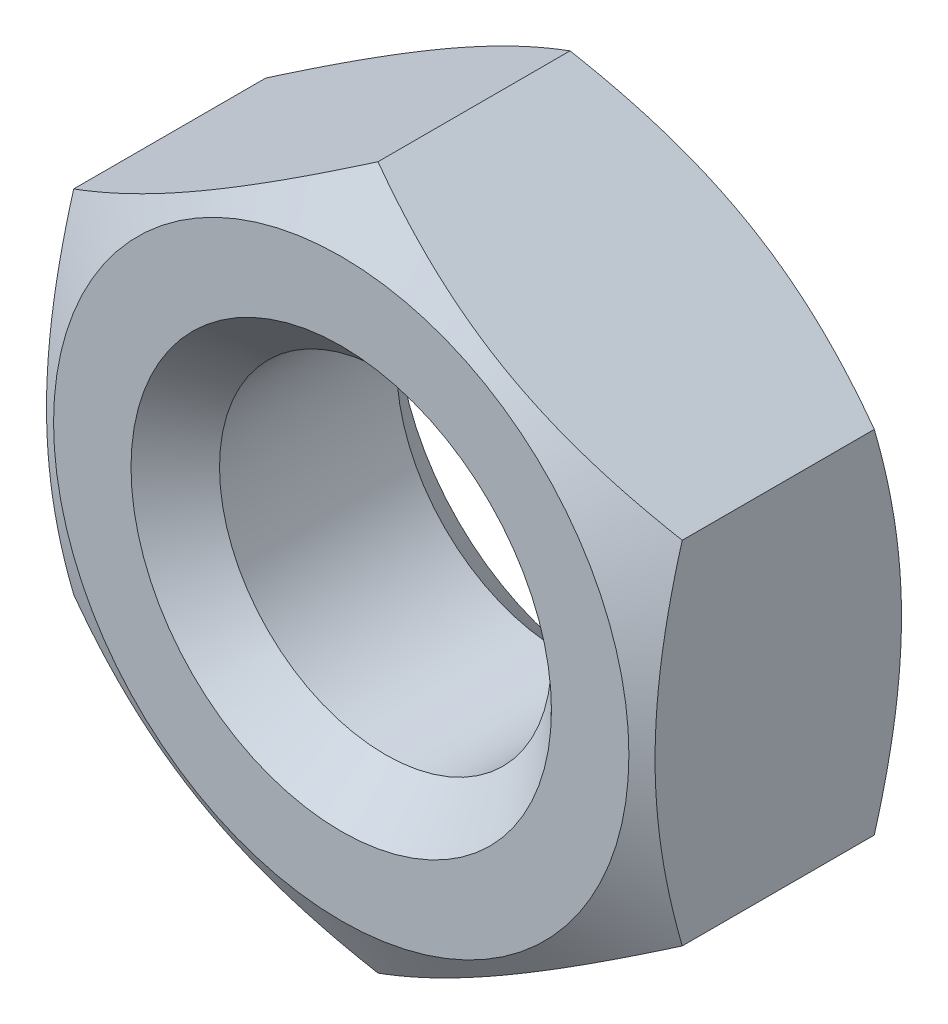
SolidWorks part; units mm, degrees
material "Простая углеродистая сталь"
ref_plane "Спереди" through (0, 0, 0) normal (0, 0, 1) x (1, 0, 0)
ref_plane "Сверху" through (0, 0, 0) normal (0, 1, 0) x (1, 0, 0)
ref_plane "Справа" through (0, 0, 0) normal (1, 0, 0) x (0, 0, -1)
sketch "Эскиз1" plane through (0, 0, 0) normal (0, 1, 0) x (1, 0, 0)
  line L1 (0, 0) -> (-4, 0)
  line L2 (0, 0) -> (0, 2.4)
  line L3 (0, 2.4) -> (-4, 2.4)
  line L4 (-4, 0) -> (-4, 2.4)
  dimension "D1" = 2.4
  dimension "D2" = 4
revolve "Повернуть1" add sketch "Эскиз1" angle 360 about L2
sketch "Эскиз2" plane through (0, 0, 0) normal (0, 0, 1) x (1, 0, 0)
  line L7 (2.75, -1.5877) -> (2.75, 1.5877)
  line L8 (2.75, 1.5877) -> (0, 3.1754)
  line L9 (0, 3.1754) -> (-2.75, 1.5877)
  line L10 (-2.75, 1.5877) -> (-2.75, -1.5877)
  line L11 (-2.75, -1.5877) -> (0, -3.1754)
  line L12 (0, -3.1754) -> (2.75, -1.5877)
  circle A0 centre (0, 0) radius 2.75 construction
  dimension "D1" = 2.75
extrude "Вырез-Вытянуть1" cut sketch "Эскиз2" against normal up to surface (2.4 mm away) flip side to cut up to face at (4, 0, -2.4)
sketch "Эскиз3" plane through (0, 0, 0) normal (0, 0, 1) x (1, 0, 0)
  circle A0 centre (0, 0) radius 1.5
  dimension "D1" = 3
extrude "Вырез-Вытянуть2" cut sketch "Эскиз3" against normal through all both and the other way through all
sketch "Эскиз4" plane through (0, 0, 0) normal (1, 0, 0) x (0, 0, -1)
  line L0 (0, 2.6) -> (0.3322, 3.1754)
  line L1 (0, 1.5877) -> (0, 3.1754) construction
  line L2 (2.4, 3.1754) -> (0, 3.1754) construction
  line L3 (0.3322, 3.1754) -> (0, 3.1754)
  line L4 (0, 3.1754) -> (0, 2.6)
  line L5 (1.2, 8.7184) -> (1.2, -2.1993) construction
  line L6 (2.4, 2.6) -> (2.0678, 3.1754)
  line L7 (2.4, 3.1754) -> (2.4, 2.6)
  line L8 (2.0678, 3.1754) -> (2.4, 3.1754)
  line L9 (0, 0) -> (50000, 0) construction
  dimension "D1" = 2.6
  dimension "D2" = 30
  dimension "D3" = 1.2
revolve "Вырез-Повернуть1" cut sketch "Эскиз4" angle 360 about L9
chamfer "Фаска1" distance 0.4 angle 45 2 edges at (-1.5, 0, 0) (1.5, 0, -2.4)
